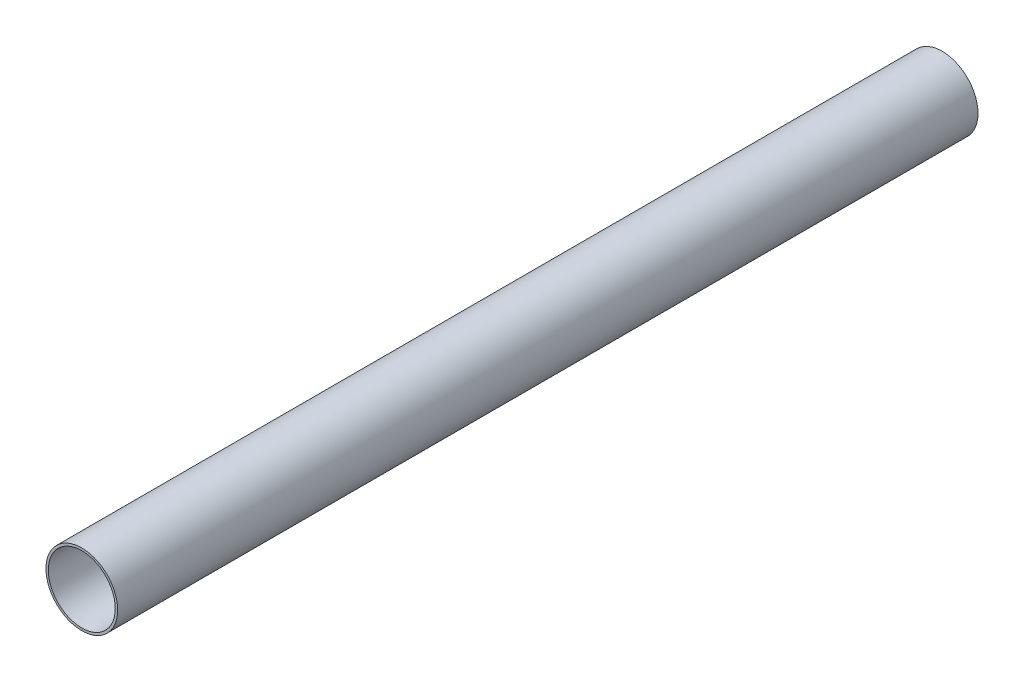
SolidWorks part; units mm, degrees
ref_plane "Front" through (0, 0, 0) normal (0, 0, 1) x (1, 0, 0)
ref_plane "Top" through (0, 0, 0) normal (0, 1, 0) x (1, 0, 0)
ref_plane "Side" through (0, 0, 0) normal (1, 0, 0) x (0, 0, -1)
sketch "PipeSketch" plane through (0, 0, 0) normal (0, 0, 1) x (1, 0, 0)
  circle A0 centre (0, 0) radius 228.6
  circle A1 centre (0, 0) radius 213.5124
  dimension "OuterDiameter" = 457.2
  dimension "InnerDiameter" = 427.0248
extrude "Extrusion" add sketch "PipeSketch" along normal blind 5486.4
sketch "FilterSketch" plane through (0, 0, 0) normal (0, 0, 1) x (1, 0, 0)
  circle A0 centre (0, 0) radius 228.6 construction
  dimension "NominalDiameter" = 457.2
